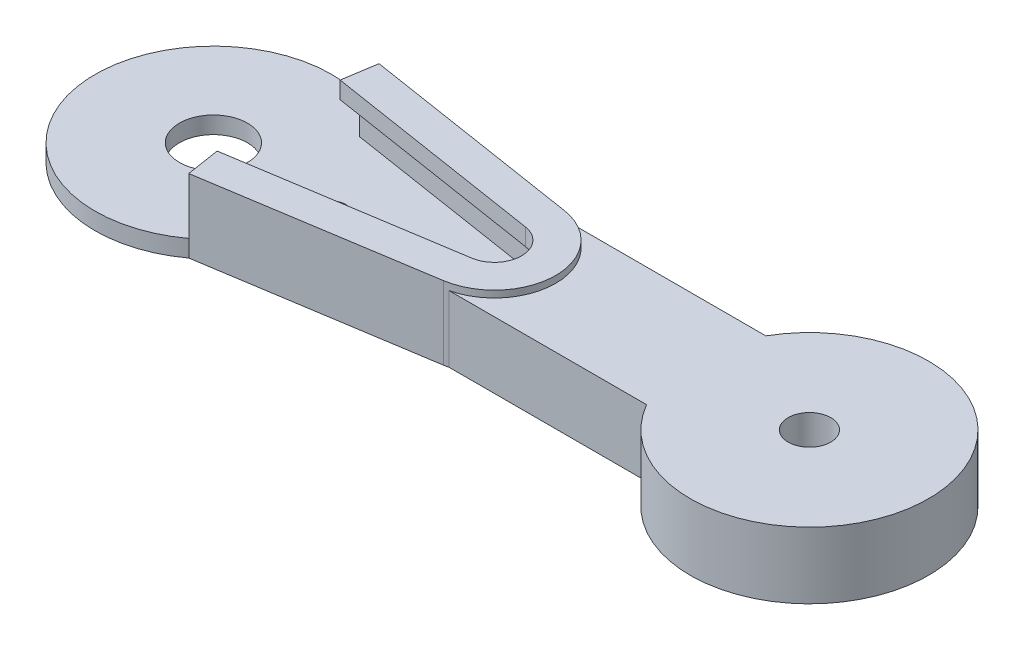
SolidWorks part; units mm, degrees
ref_plane "Front Plane" through (0, 0, 0) normal (0, 0, 1) x (1, 0, 0)
ref_plane "Top Plane" through (0, 0, 0) normal (0, 1, 0) x (1, 0, 0)
ref_plane "Right Plane" through (0, 0, 0) normal (1, 0, 0) x (0, 0, -1)
sketch "Sketch2" plane through (0, 0, 0) normal (0, 1, 0) x (1, 0, 0)
  circle A0 centre (0, 0) radius 6
  circle A1 centre (0, 0) radius 1.5
  dimension "D1" = 12
  dimension "D2" = 3
extrude "Boss-Extrude1" add sketch "Sketch2" along normal mid plane 2.3
sketch "Sketch3" plane through (0, 1.15, 0) normal (0, 1, 0) x (1, 0, 0)
  line L0 (0, 0) -> (0, 2.9) construction
  line L3 (0, 0) -> (0.376, 2.9763) construction
  line L52 (0.1074, 2.898) -> (0.3384, 2.6787)
  line L53 (-0.1074, 2.898) -> (-0.3384, 2.6787)
  line L54 (0.8248, 2.7802) -> (0.9939, 2.5104)
  line L55 (0.6167, 2.8337) -> (0.3384, 2.6787)
  line L56 (1.4903, 2.4878) -> (1.587, 2.1843)
  line L57 (1.302, 2.5913) -> (0.9939, 2.5104)
  line L58 (2.0621, 2.039) -> (2.0804, 1.721)
  line L59 (1.9055, 2.1861) -> (1.587, 2.1843)
  line L60 (2.5044, 1.4621) -> (2.443, 1.1496)
  line L61 (2.3893, 1.6435) -> (2.0804, 1.721)
  line L62 (2.7894, 0.7934) -> (2.6522, 0.5059)
  line L63 (2.723, 0.9977) -> (2.443, 1.1496)
  line L64 (2.899, 0.0748) -> (2.6947, -0.1695)
  line L65 (2.8855, 0.2892) -> (2.6522, 0.5059)
  line L66 (2.8265, -0.6486) -> (2.5679, -0.8343)
  line L67 (2.8668, -0.4375) -> (2.6947, -0.1695)
  line L68 (2.5765, -1.3311) -> (2.2797, -1.4467)
  line L69 (2.6679, -1.1367) -> (2.5679, -0.8343)
  line L70 (2.1645, -1.93) -> (1.8483, -1.9682)
  line L71 (2.3014, -1.7645) -> (2.2797, -1.4467)
  line L72 (1.6165, -2.4077) -> (1.3007, -2.366)
  line L73 (1.7903, -2.2814) -> (1.8483, -1.9682)
  line L74 (0.967, -2.734) -> (0.6715, -2.6152)
  line L75 (1.1667, -2.655) -> (1.3007, -2.366)
  line L76 (0.2566, -2.8886) -> (0, -2.7)
  line L77 (0.4698, -2.8617) -> (0.6715, -2.6152)
  line L78 (-0.4698, -2.8617) -> (-0.6715, -2.6152)
  line L79 (-0.2566, -2.8886) -> (0, -2.7)
  line L80 (-1.1667, -2.655) -> (-1.3007, -2.366)
  line L81 (-0.967, -2.734) -> (-0.6715, -2.6152)
  line L82 (-1.7903, -2.2814) -> (-1.8483, -1.9682)
  line L83 (-1.6165, -2.4077) -> (-1.3007, -2.366)
  line L84 (-2.3014, -1.7645) -> (-2.2797, -1.4467)
  line L85 (-2.1645, -1.93) -> (-1.8483, -1.9682)
  line L86 (-2.6679, -1.1367) -> (-2.5679, -0.8343)
  line L87 (-2.5765, -1.3311) -> (-2.2797, -1.4467)
  line L88 (-2.8668, -0.4375) -> (-2.6947, -0.1695)
  line L89 (-2.8265, -0.6486) -> (-2.5679, -0.8343)
  line L90 (-2.8855, 0.2892) -> (-2.6522, 0.5059)
  line L91 (-2.899, 0.0748) -> (-2.6947, -0.1695)
  line L92 (-2.723, 0.9977) -> (-2.443, 1.1496)
  line L93 (-2.7894, 0.7934) -> (-2.6522, 0.5059)
  line L94 (-2.3893, 1.6435) -> (-2.0804, 1.721)
  line L95 (-2.5044, 1.4621) -> (-2.443, 1.1496)
  line L96 (-1.9055, 2.1861) -> (-1.587, 2.1843)
  line L97 (-2.0621, 2.039) -> (-2.0804, 1.721)
  line L98 (-1.302, 2.5913) -> (-0.9939, 2.5104)
  line L99 (-1.4903, 2.4878) -> (-1.587, 2.1843)
  line L100 (-0.6167, 2.8337) -> (-0.3384, 2.6787)
  line L101 (-0.8248, 2.7802) -> (-0.9939, 2.5104)
  line L102 (-2.533, 1.6075) -> (-2.3893, 1.6435) construction
  line L103 (-2.533, 1.6075) -> (-2.5044, 1.4621) construction
  line L104 (-2.8532, 0.9271) -> (-2.723, 0.9977) construction
  line L105 (-2.8532, 0.9271) -> (-2.7894, 0.7934) construction
  line L106 (-2.9941, 0.1884) -> (-2.8855, 0.2892) construction
  line L107 (-2.9941, 0.1884) -> (-2.899, 0.0748) construction
  line L108 (-2.9469, -0.5621) -> (-2.8668, -0.4375) construction
  line L109 (-2.9469, -0.5621) -> (-2.8265, -0.6486) construction
  line L110 (0, 3) -> (0.1074, 2.898) construction
  line L111 (0, 2.9) -> (0, 3) construction
  line L112 (0, 3) -> (-0.1074, 2.898) construction
  line L113 (-0.7461, 2.9057) -> (-0.6167, 2.8337) construction
  line L114 (-0.7461, 2.9057) -> (-0.8248, 2.7802) construction
  line L115 (-1.4453, 2.6289) -> (-1.302, 2.5913) construction
  line L116 (-1.4453, 2.6289) -> (-1.4903, 2.4878) construction
  line L117 (-2.0536, 2.1869) -> (-1.9055, 2.1861) construction
  line L118 (-2.0536, 2.1869) -> (-2.0621, 2.039) construction
  line L119 (-2.7145, -1.2773) -> (-2.6679, -1.1367) construction
  line L120 (-2.7145, -1.2773) -> (-2.5765, -1.3311) construction
  line L121 (-2.3115, -1.9123) -> (-2.3014, -1.7645) construction
  line L122 (-2.3115, -1.9123) -> (-2.1645, -1.93) construction
  line L123 (-1.7634, -2.4271) -> (-1.7903, -2.2814) construction
  line L124 (-1.7634, -2.4271) -> (-1.6165, -2.4077) construction
  line L125 (-1.1044, -2.7893) -> (-1.1667, -2.655) construction
  line L126 (-1.1044, -2.7893) -> (-0.967, -2.734) construction
  line L127 (-0.376, -2.9763) -> (-0.4698, -2.8617) construction
  line L128 (-0.376, -2.9763) -> (-0.2566, -2.8886) construction
  line L129 (0.376, -2.9763) -> (0.2566, -2.8886) construction
  line L130 (0.376, -2.9763) -> (0.4698, -2.8617) construction
  line L131 (1.1044, -2.7893) -> (0.967, -2.734) construction
  line L132 (1.1044, -2.7893) -> (1.1667, -2.655) construction
  line L133 (1.7634, -2.4271) -> (1.6165, -2.4077) construction
  line L134 (1.7634, -2.4271) -> (1.7903, -2.2814) construction
  line L135 (2.3115, -1.9123) -> (2.3014, -1.7645) construction
  line L136 (2.3115, -1.9123) -> (2.1645, -1.93) construction
  line L137 (2.7145, -1.2773) -> (2.6679, -1.1367) construction
  line L138 (2.7145, -1.2773) -> (2.5765, -1.3311) construction
  line L139 (2.9469, -0.5621) -> (2.8668, -0.4375) construction
  line L140 (2.9469, -0.5621) -> (2.8265, -0.6486) construction
  line L141 (2.9941, 0.1884) -> (2.8855, 0.2892) construction
  line L142 (2.9941, 0.1884) -> (2.899, 0.0748) construction
  line L143 (2.8532, 0.9271) -> (2.723, 0.9977) construction
  line L144 (2.8532, 0.9271) -> (2.7894, 0.7934) construction
  line L145 (2.533, 1.6075) -> (2.3893, 1.6435) construction
  line L146 (2.533, 1.6075) -> (2.5044, 1.4621) construction
  line L147 (2.0536, 2.1869) -> (1.9055, 2.1861) construction
  line L148 (2.0536, 2.1869) -> (2.0621, 2.039) construction
  line L149 (1.4453, 2.6289) -> (1.302, 2.5913) construction
  line L150 (1.4453, 2.6289) -> (1.4903, 2.4878) construction
  line L151 (0.7461, 2.9057) -> (0.6167, 2.8337) construction
  line L152 (0.7461, 2.9057) -> (0.8248, 2.7802) construction
  circle A0 centre (0, 0) radius 4.4
  circle A1 centre (0, 0) radius 3 construction
  circle A2 centre (0, 0) radius 2.7 construction
  arc A3 (-0.6167, 2.8337) -> (-0.8248, 2.7802) centre (0, 0) ccw
  arc A4 (-0.1074, 2.898) -> (-0.6167, 2.8337) centre (0, 0) ccw construction
  arc A5 (-0.8248, 2.7802) -> (-1.302, 2.5913) centre (0, 0) ccw construction
  arc A6 (-1.302, 2.5913) -> (-1.4903, 2.4878) centre (0, 0) ccw
  arc A7 (-1.4903, 2.4878) -> (-1.9055, 2.1861) centre (0, 0) ccw construction
  arc A8 (-1.9055, 2.1861) -> (-2.0621, 2.039) centre (0, 0) ccw
  arc A9 (-2.0621, 2.039) -> (-2.3893, 1.6435) centre (0, 0) ccw construction
  arc A10 (-2.3893, 1.6435) -> (-2.5044, 1.4621) centre (0, 0) ccw
  arc A11 (-2.5044, 1.4621) -> (-2.723, 0.9977) centre (0, 0) ccw construction
  arc A12 (-2.723, 0.9977) -> (-2.7894, 0.7934) centre (0, 0) ccw
  arc A13 (-2.7894, 0.7934) -> (-2.8855, 0.2892) centre (0, 0) ccw construction
  arc A14 (-2.8855, 0.2892) -> (-2.899, 0.0748) centre (0, 0) ccw
  arc A15 (-2.899, 0.0748) -> (-2.8668, -0.4375) centre (0, 0) ccw construction
  arc A16 (-2.8668, -0.4375) -> (-2.8265, -0.6486) centre (0, 0) ccw
  arc A17 (-2.8265, -0.6486) -> (-2.6679, -1.1367) centre (0, 0) ccw construction
  arc A18 (-2.6679, -1.1367) -> (-2.5765, -1.3311) centre (0, 0) ccw
  arc A19 (-2.5765, -1.3311) -> (-2.3014, -1.7645) centre (0, 0) ccw construction
  arc A20 (-2.3014, -1.7645) -> (-2.1645, -1.93) centre (0, 0) ccw
  arc A21 (-2.1645, -1.93) -> (-1.7903, -2.2814) centre (0, 0) ccw construction
  arc A22 (-1.7903, -2.2814) -> (-1.6165, -2.4077) centre (0, 0) ccw
  arc A23 (-1.6165, -2.4077) -> (-1.1667, -2.655) centre (0, 0) ccw construction
  arc A24 (-1.1667, -2.655) -> (-0.967, -2.734) centre (0, 0) ccw
  arc A25 (-0.967, -2.734) -> (-0.4698, -2.8617) centre (0, 0) ccw construction
  arc A26 (-0.4698, -2.8617) -> (-0.2566, -2.8886) centre (0, 0) ccw
  arc A27 (-0.2566, -2.8886) -> (0.2566, -2.8886) centre (0, 0) ccw construction
  arc A28 (0.2566, -2.8886) -> (0.4698, -2.8617) centre (0, 0) ccw
  arc A29 (0.4698, -2.8617) -> (0.967, -2.734) centre (0, 0) ccw construction
  arc A30 (0.967, -2.734) -> (1.1667, -2.655) centre (0, 0) ccw
  arc A31 (1.1667, -2.655) -> (1.6165, -2.4077) centre (0, 0) ccw construction
  arc A32 (1.6165, -2.4077) -> (1.7903, -2.2814) centre (0, 0) ccw
  arc A33 (1.7903, -2.2814) -> (2.1645, -1.93) centre (0, 0) ccw construction
  arc A34 (2.1645, -1.93) -> (2.3014, -1.7645) centre (0, 0) ccw
  arc A35 (2.3014, -1.7645) -> (2.5765, -1.3311) centre (0, 0) ccw construction
  arc A36 (2.5765, -1.3311) -> (2.6679, -1.1367) centre (0, 0) ccw
  arc A37 (2.6679, -1.1367) -> (2.8265, -0.6486) centre (0, 0) ccw construction
  arc A38 (2.8265, -0.6486) -> (2.8668, -0.4375) centre (0, 0) ccw
  arc A39 (2.8668, -0.4375) -> (2.899, 0.0748) centre (0, 0) ccw construction
  arc A40 (2.899, 0.0748) -> (2.8855, 0.2892) centre (0, 0) ccw
  arc A41 (2.8855, 0.2892) -> (2.7894, 0.7934) centre (0, 0) ccw construction
  arc A42 (2.7894, 0.7934) -> (2.723, 0.9977) centre (0, 0) ccw
  arc A43 (2.723, 0.9977) -> (2.5044, 1.4621) centre (0, 0) ccw construction
  arc A44 (2.5044, 1.4621) -> (2.3893, 1.6435) centre (0, 0) ccw
  arc A45 (2.3893, 1.6435) -> (2.0621, 2.039) centre (0, 0) ccw construction
  arc A46 (2.0621, 2.039) -> (1.9055, 2.1861) centre (0, 0) ccw
  arc A47 (1.9055, 2.1861) -> (1.4903, 2.4878) centre (0, 0) ccw construction
  arc A48 (1.4903, 2.4878) -> (1.302, 2.5913) centre (0, 0) ccw
  arc A49 (1.302, 2.5913) -> (0.8248, 2.7802) centre (0, 0) ccw construction
  arc A50 (0.8248, 2.7802) -> (0.6167, 2.8337) centre (0, 0) ccw
  arc A51 (0.3635, 2.8771) -> (0.1074, 2.898) centre (0, 0) ccw construction
  arc A52 (0.1074, 2.898) -> (-0.1074, 2.898) centre (0, 0) ccw
  arc A53 (0.6167, 2.8337) -> (0.3635, 2.8771) centre (0, 0) ccw construction
  point P84 (0, 0)
  dimension "D1" = 8.8
  dimension "D2" = 5.4
  dimension "D3" = 6
  dimension "D6" = 5.8
  dimension "D4" = 7.2
  dimension "D5" = 25
extrude "Boss-Extrude2" add sketch "Sketch3" along normal blind 3.2
sketch "Sketch4" plane through (0, 0, 0) normal (0, 1, 0) x (1, 0, 0)
  line L0 (0, 0) -> (16, 0) construction
  line L1 (3.9686, 4.5) -> (16.8881, 2.4697)
  line L2 (3.9686, -4.5) -> (16.8881, -2.4697)
  line L3 (16, 0) -> (13, 0) construction
  circle A0 centre (0, 0) radius 6 construction
  arc A1 (3.9686, -4.5) -> (3.9686, 4.5) centre (0, 0) ccw
  arc A2 (16.8881, 2.4697) -> (16.8881, -2.4697) centre (16.5, 0) cw
  circle A3 centre (16, 0) radius 0.75
  circle A4 centre (13, 0) radius 0.75
  circle A5 centre (10, 0) radius 0.75
  circle A6 centre (7, 0) radius 0.75
  dimension "D3" = 2.5
  dimension "D5" = 1.5
  dimension "D2" = 9
  dimension "D7" = 3
  dimension "D4" = 0.5
  dimension "D1" = 16
  dimension "D6" = 4
extrude "Boss-Extrude3" add sketch "Sketch4" along normal mid plane 2.3
pattern_circular "CirPattern1" count 2 over 360 about axis through (0, 0, 0) along (0, 1, 0) of "Boss-Extrude3"
sketch "Sketch5" [suppressed] plane through (0, 0, 0) normal (0, 1, 0) x (1, 0, 0)
  line L0 (3, 7) -> (-3, 7) construction
  circle A0 centre (0, 0) radius 10
  circle A1 centre (0, 7) radius 0.75
  circle A2 centre (-3, 7) radius 0.75
  circle A3 centre (3, 7) radius 0.75
  circle A4 centre (7, 3) radius 0.75
  circle A5 centre (7, 0) radius 0.75
  circle A6 centre (7, -3) radius 0.75
  circle A7 centre (3, -7) radius 0.75
  circle A8 centre (0, -7) radius 0.75
  circle A9 centre (-3, -7) radius 0.75
  circle A10 centre (-7, -3) radius 0.75
  circle A11 centre (-7, 0) radius 0.75
  circle A12 centre (-7, 3) radius 0.75
  circle A13 centre (0, 0) radius 1.5 construction
  circle A14 centre (0, 0) radius 1.5
  point P8 (0, 7)
  point P31 (0, 0)
  dimension "D1" = 1.5
  dimension "D3" = 2.25
  dimension "D4" = 6
  dimension "D2" = 7
  dimension "D5" = 4
extrude "Boss-Extrude4" [suppressed] add sketch "Sketch5" along normal mid plane 2.3
sketch "Sketch6" plane through (0, -1.15, 0) normal (0, -1, 0) x (1, 0, 0)
  line L3 (16.9036, 2.5685) -> (3.9842, 4.5988)
  line L5 (16.9036, 2.5685) -> (3.9842, 4.5988)
  line L6 (17.0589, -3.5564) -> (4.1394, -5.5867)
  line L7 (16.9036, -2.5685) -> (3.9842, -4.5988)
  line L8 (16.9036, -2.5685) -> (3.9842, -4.5988)
  line L9 (17.0589, 3.5564) -> (4.1394, 5.5867)
  line L10 (4.1394, 5.5867) -> (3.9842, 4.5988)
  line L11 (3.9842, -4.5988) -> (4.1394, -5.5867)
  circle A3 centre (0, 0) radius 6.0846
  arc A4 (16.9036, -2.5685) -> (16.9036, 2.5685) centre (16.5, 0) ccw
  arc A5 (16.9036, -2.5685) -> (16.9036, 2.5685) centre (16.5, 0) ccw
  arc A6 (17.0589, -3.5564) -> (17.0589, 3.5564) centre (16.5, 0) ccw
  dimension "D1" = 0.1
  dimension "D2" = 0.1
  dimension "D3" = 1
extrude "Boss-Extrude5" add sketch "Sketch6" against normal blind 2.3 separate body contours L6 A6 L9 L10 L5 A5 L8 L11
sketch "Sketch7" plane through (0, -1.15, 0) normal (0, -1, 0) x (1, 0, 0)
  line L14 (4.1394, -5.5867) -> (17.0589, -3.5564)
  line L15 (17.0589, 3.5564) -> (4.1394, 5.5867)
  line L16 (4.1394, -5.5867) -> (17.0589, -3.5564)
  line L17 (17.0589, 3.5564) -> (4.1394, 5.5867)
  arc A2 (4.1394, 5.5867) -> (4.1394, -5.5867) centre (0, 0) ccw
  circle A5 centre (0, 0) radius 2
  arc A6 (17.0589, -3.5564) -> (17.0589, 3.5564) centre (16.5, 0) ccw
  arc A7 (17.0589, -3.5564) -> (17.0589, 3.5564) centre (16.5, 0) ccw
  dimension "D1" = 1
extrude "Boss-Extrude6" add sketch "Sketch7" along normal blind 1
sketch "Sketch10" plane through (0, -2.15, 0) normal (0, -1, 0) x (1, 0, 0)
  line L0 (0, 0) -> (20.1, 0) construction
  arc A0 (17.0589, -3.5564) -> (17.0589, 3.5564) centre (16.5, 0) ccw construction
  circle A3 centre (7, 0) radius 0.75
  circle A4 centre (10, 0) radius 0.75
  circle A5 centre (13, 0) radius 0.75
  circle A6 centre (16, 0) radius 0.75
  dimension "D1" = 1.5
  dimension "D2" = 7
  dimension "D3" = 4
extrude "Cut-Extrude2" cut sketch "Sketch10" against normal through all contours L0 A4 | L0 A5 | L0 A6 | A6 L0 | A5 L0 | A4 L0 | A3 L0 | L0 A3
sketch "Sketch12" plane through (0, 1.15, 0) normal (0, 1, 0) x (1, 0, 0)
  line L8 (-3.9686, 4.5) -> (-16.8881, 2.4697)
  line L9 (-16.8881, -2.4697) -> (-3.9686, -4.5)
  line L10 (3.9686, -4.5) -> (16.8881, -2.4697)
  line L12 (-3.9686, 4.5) -> (-16.8881, 2.4697)
  line L13 (-16.8881, -2.4697) -> (-3.9686, -4.5)
  line L16 (3.9686, -4.5) -> (16.8881, -2.4697)
  line L17 (16.8881, 2.4697) -> (3.9686, 4.5)
  line L18 (16.8881, 2.4697) -> (3.9686, 4.5)
  arc A8 (3.9686, 4.5) -> (-3.9686, 4.5) centre (0, 0) ccw
  arc A9 (-16.8881, 2.4697) -> (-16.8881, -2.4697) centre (-16.5, 0) ccw
  arc A10 (-3.9686, -4.5) -> (3.9686, -4.5) centre (0, 0) ccw
  arc A11 (16.8881, -2.4697) -> (16.8881, 2.4697) centre (16.5, 0) ccw
  arc A12 (3.9686, 4.5) -> (-3.9686, 4.5) centre (0, 0) ccw
  arc A13 (-16.8881, 2.4697) -> (-16.8881, -2.4697) centre (-16.5, 0) ccw
  arc A14 (-3.9686, -4.5) -> (3.9686, -4.5) centre (0, 0) ccw
  arc A17 (16.8881, -2.4697) -> (16.8881, 2.4697) centre (16.5, 0) ccw
  dimension "D1" = 0
extrude "Cut-Extrude4" cut sketch "Sketch12" against normal blind 2.3
sketch "Sketch13" plane through (0, 4.35, 0) normal (0, 1, 0) x (1, 0, 0)
  circle A3 centre (0, 0) radius 4.4
  circle A4 centre (0, 0) radius 4.4
  dimension "D1" = 0
extrude "Cut-Extrude5" cut sketch "Sketch13" against normal blind 3.3
sketch "Sketch9" plane through (0, 1.15, 0) normal (0, 1, 0) x (1, 0, 0)
  line L0 (3.8289, -3.6109) -> (16.7484, -1.5806)
  line L1 (16.7484, 1.5806) -> (3.8289, 3.6109)
  line L2 (3.8289, 3.6109) -> (3.9842, 4.5988)
  line L3 (3.8289, -3.6109) -> (3.9842, -4.5988)
  line L5 (4.1394, 5.5867) -> (3.9842, 4.5988)
  line L7 (4.1394, -5.5867) -> (17.0589, -3.5564)
  line L8 (17.0589, 3.5564) -> (4.1394, 5.5867)
  line L9 (4.1394, -5.5867) -> (17.0589, -3.5564)
  line L10 (17.0589, 3.5564) -> (4.1394, 5.5867)
  line L11 (3.9842, -4.5988) -> (4.1394, -5.5867)
  line L30 (3.9842, -4.5988) -> (16.9036, -2.5685)
  line L31 (16.9036, 2.5685) -> (3.9842, 4.5988)
  line L32 (3.9842, -4.5988) -> (16.9036, -2.5685)
  line L33 (16.9036, 2.5685) -> (3.9842, 4.5988)
  arc A0 (16.7484, -1.5806) -> (16.7484, 1.5806) centre (16.5, 0) ccw
  arc A2 (17.0589, -3.5564) -> (17.0589, 3.5564) centre (16.5, 0) ccw
  arc A3 (17.0589, -3.5564) -> (17.0589, 3.5564) centre (16.5, 0) ccw
  arc A9 (16.9036, -2.5685) -> (16.9036, 2.5685) centre (16.5, 0) ccw
  arc A10 (16.9036, -2.5685) -> (16.9036, 2.5685) centre (16.5, 0) ccw
  line M4 (17.0589, 3.5564) -> (4.1394, 5.5867)
  line M5 (4.1394, 5.5867) -> (3.9842, 4.5988)
  line M6 (3.9842, 4.5988) -> (16.9036, 2.5685)
  arc M7 (16.9036, 2.5685) -> (16.9036, -2.5685) centre (16.5, 0) cw
  line M8 (16.9036, -2.5685) -> (3.9842, -4.5988)
  line M9 (3.9842, -4.5988) -> (4.1394, -5.5867)
  line M10 (4.1394, -5.5867) -> (17.0589, -3.5564)
  arc M11 (17.0589, -3.5564) -> (17.0589, 3.5564) centre (16.5, 0) ccw
  dimension "D1" = 1
  dimension "D2" = 0
  dimension "D3" = 1
extrude "Boss-Extrude8" add sketch "Sketch9" along normal blind 1 contours M11 M4 M5 M6 M7 M8 M9 M10 | A0 L0 L3 L2 L1 M8 M7 M6
sketch "Sketch14" plane through (0, -2.15, 0) normal (0, -1, 0) x (1, 0, 0)
  line L0 (0, 0) -> (35, 0) construction
  line L1 (17.0589, 3.5564) -> (17.0589, -3.5564) construction
  line L3 (17.0589, 0) -> (30.837, 0)
  line L4 (17.0589, 0) -> (17.0589, 3.5)
  line L5 (17.0589, 3.5) -> (30.837, 3.5)
  line L6 (30.837, 0) -> (30.837, 3.5)
  line L7 (17.0589, 0) -> (30.837, 0)
  line L8 (17.0589, 0) -> (17.0589, -3.5)
  line L9 (17.0589, -3.5) -> (30.837, -3.5)
  line L10 (30.837, 0) -> (30.837, -3.5)
  circle A0 centre (35, 0) radius 7
  circle A1 centre (35, 0) radius 1.25
  arc M7 (17.0589, -3.5564) -> (17.0589, 3.5564) centre (16.5, 0) ccw
  dimension "D2" = 2.5
  dimension "D1" = 35
  dimension "D3" = 3.5
  dimension "D4" = 3.5
extrude "Boss-Extrude9" add sketch "Sketch14" against normal blind 3.9 contours A0 L3 L9 M7 | A0 L5 L3 M7 | L9 A0 L5 L6 L10 A1 | L7 A0 L9 L10 | L5 A0 L7 L6
equation "\"N_hole\"= 4"
equation "\"N_horn\"= 2"
equation "\"D6@Sketch4\"=\"N_hole\""
equation "\"D1@CirPattern1\"=\"N_horn\""
equation "\"D1@Sketch4\"=(\"N_hole\" - 1) *3 +7"
